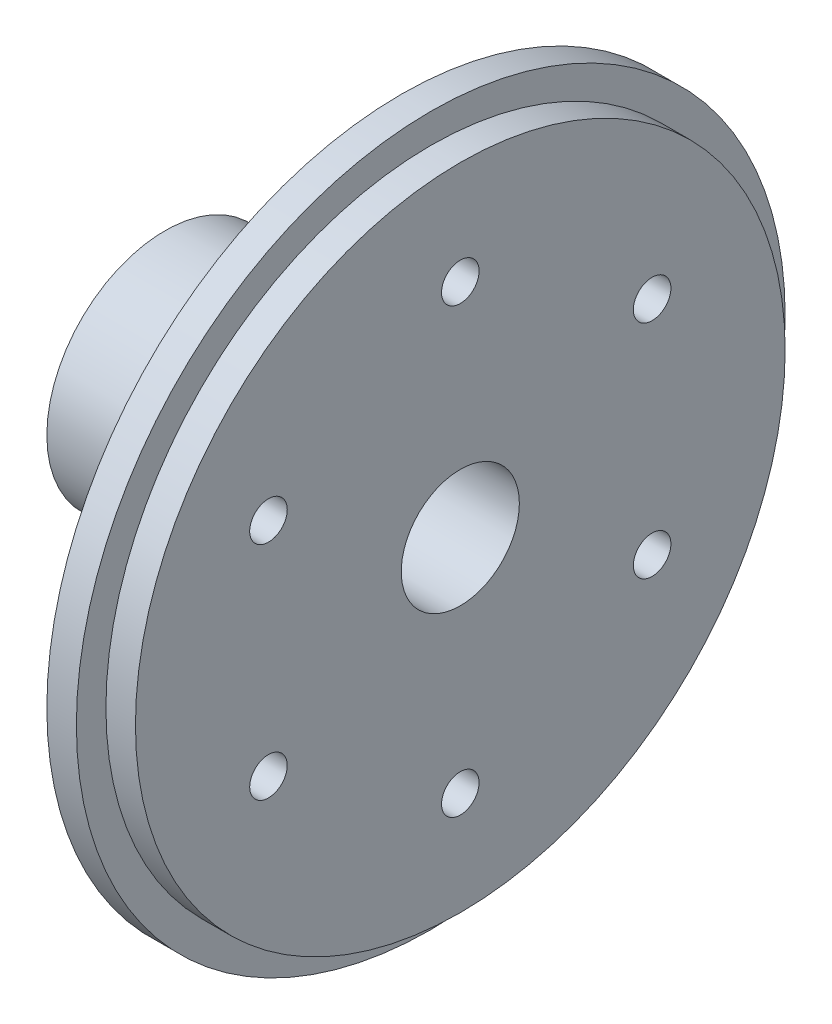
SolidWorks part; units mm, degrees
ref_plane "Front Plane" through (0, 0, 0) normal (0, 0, 1) x (1, 0, 0)
ref_plane "Top Plane" through (0, 0, 0) normal (0, 1, 0) x (1, 0, 0)
ref_plane "Right Plane" through (0, 0, 0) normal (1, 0, 0) x (0, 0, -1)
sketch "Sketch1" plane through (0, 0, 0) normal (1, 0, 0) x (0, 0, -1)
  circle A0 centre (0, 0) radius 38.1
  dimension "D1" = 76.2
extrude "Boss-Extrude1" add sketch "Sketch1" along normal blind 6.35
sketch "Sketch3" plane through (6.35, 0, 0) normal (1, 0, 0) x (0, 0, -1)
  circle A0 centre (0, 0) radius 38.1 construction
  circle A1 centre (0, 0) radius 38.1
extrude "Cut-Extrude-Thin1" cut sketch "Sketch3" against normal blind 3.175 thin thin type one direction reverse wall 3.175
sketch "Sketch8" plane through (0, 0, 0) normal (-1, 0, 0) x (0, 0, 1)
  circle A0 centre (0, 0) radius 12.7
  dimension "D1" = 25.4
extrude "Boss-Extrude2" add sketch "Sketch8" along normal blind 25.4
hole_wizard "1/2 (0.5) Diameter Hole1" positions "Sketch4" profile "Sketch5" hole size "1/2" standard "ANSI Inch" end condition through all
sketch "Sketch4" plane through (6.35, 0, 0) normal (1, 0, 0) x (0, 0, -1)
  point P0 (0, 0)
sketch "Sketch5" plane through (6.35, 0, 0) normal (0, 1, 0) x (0, 0, -1)
  line L0 (0, 0) -> (0, 31.75)
  line L1 (0, 31.75) -> (6.35, 31.75)
  line L2 (6.35, 31.75) -> (6.35, 0)
  line L5 (6.35, 0) -> (0, 0)
  line L11 (0, -6.35) -> (0, 107.95) construction
  dimension "Thru Hole Dia." = 12.7
  dimension "Thru Hole Depth" = 31.75
hole_wizard "#10-32 Tapped Hole1" positions "Sketch6" profile "Sketch7" tap size "#10-32" standard "ANSI Inch" end condition through all
sketch "Sketch6" plane through (0, 0, 0) normal (-1, 0, 0) x (0, 0, 1)
  point P0 (0, 23.8125)
  dimension "D1" = 23.8125
sketch "Sketch7" plane through (0, 23.8125, 0) normal (0, 1, 0) x (0, 0, 1)
  line L0 (0, 0) -> (0, 6.35)
  line L1 (0, 6.35) -> (2.0193, 6.35)
  line L2 (2.0193, 6.35) -> (2.0193, 0)
  line L5 (2.0193, 0) -> (0, 0)
  line L11 (0, -6.35) -> (0, 107.95) construction
  dimension "Thru Tap Drill Dia." = 4.0386
  dimension "Thru Tap Drill Depth" = 6.35
cosmetic thread "Hole Thread1" parameters "D2"=4.826
pattern_circular "CirPattern1" count 6 over 360 about axis through (0, 0, 0) along (1, 0, 0) of "#10-32 Tapped Hole1"
